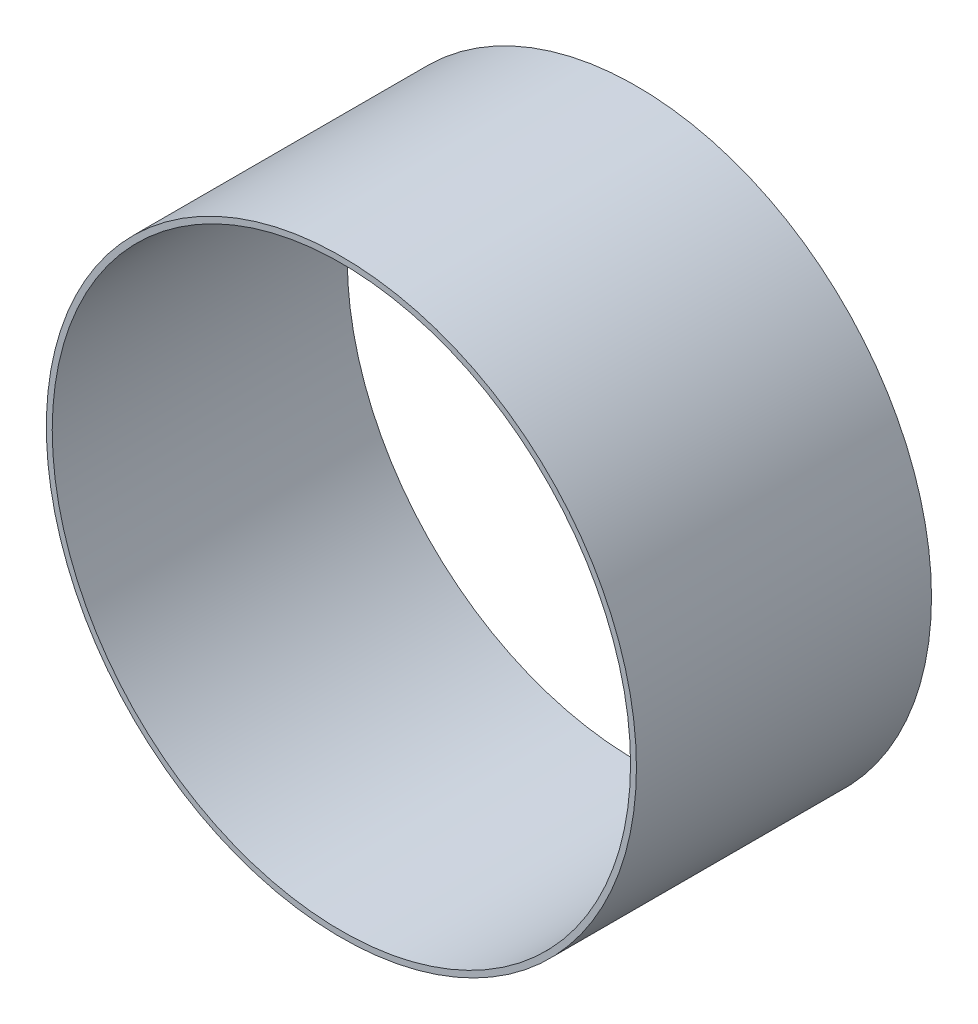
SolidWorks part; units mm, degrees
ref_plane "前视基准面" through (0, 0, 0) normal (0, 0, 1) x (1, 0, 0)
ref_plane "上视基准面" through (0, 0, 0) normal (0, 1, 0) x (1, 0, 0)
ref_plane "右视基准面" through (0, 0, 0) normal (1, 0, 0) x (0, 0, -1)
sketch "草图1" plane through (0, 0, 0) normal (0, 0, 1) x (1, 0, 0)
  circle A0 centre (0, 0) radius 100
  circle A1 centre (0, 0) radius 98
  dimension "D1" = 200
  dimension "D2" = 196
extrude "凸台-拉伸1" add sketch "草图1" along normal blind 100
ref_plane "基准面1" through (0, 0, 0) normal (1, 0, 0) x (0, 0, -1)
